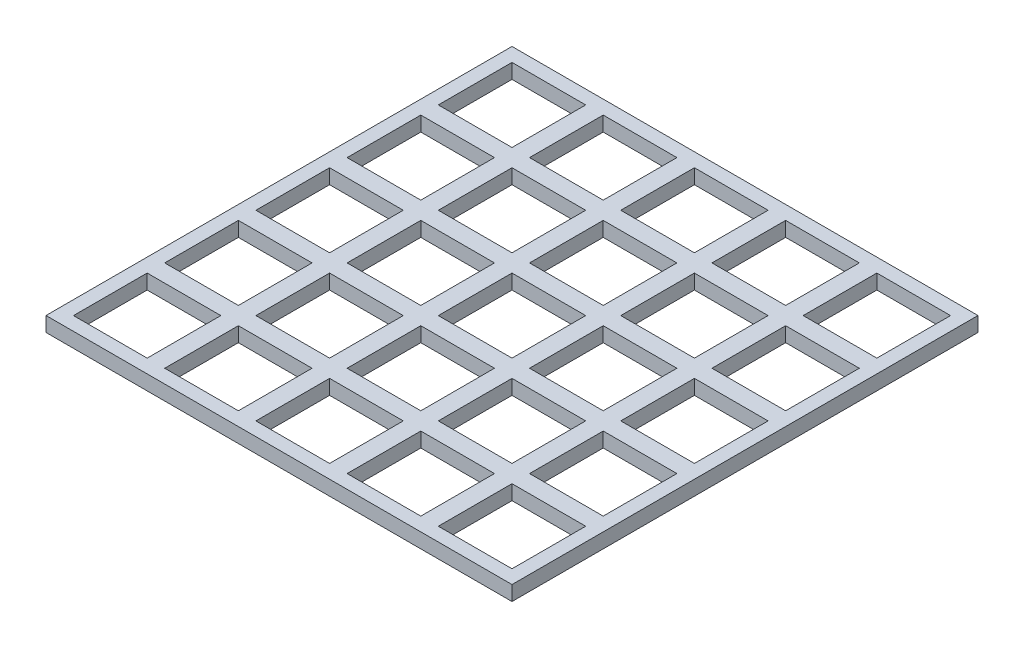
SolidWorks part; units mm, degrees
ref_plane "Front Plane" through (0, 0, 0) normal (0, 0, 1) x (1, 0, 0)
ref_plane "Top Plane" through (0, 0, 0) normal (0, 1, 0) x (1, 0, 0)
ref_plane "Right Plane" through (0, 0, 0) normal (1, 0, 0) x (0, 0, -1)
sketch "Sketch3" plane through (0, 0, 0) normal (0, 1, 0) x (1, 0, 0)
  line L0 (-17.245, 29.875) -> (-7.245, 29.875)
  line L1 (-31.5, 31.75) -> (31.75, 31.75)
  line L2 (-31.5, 31.75) -> (-31.5, -31.5)
  line L3 (-31.5, -31.5) -> (31.75, -31.5)
  line L4 (31.75, 31.75) -> (31.75, -31.5)
  line L5 (-29.625, 29.875) -> (-19.625, 29.875)
  line L6 (-29.625, 29.875) -> (-29.625, 19.875)
  line L7 (-29.625, 19.875) -> (-19.625, 19.875)
  line L8 (-19.625, 29.875) -> (-19.625, 19.875)
  line L9 (-17.245, 29.875) -> (-17.245, 19.875)
  line L10 (-17.245, 19.875) -> (-7.245, 19.875)
  line L11 (-7.245, 29.875) -> (-7.245, 19.875)
  line L12 (-4.865, 29.875) -> (5.135, 29.875)
  line L13 (-4.865, 29.875) -> (-4.865, 19.875)
  line L14 (-4.865, 19.875) -> (5.135, 19.875)
  line L15 (5.135, 29.875) -> (5.135, 19.875)
  line L16 (7.515, 29.875) -> (17.515, 29.875)
  line L17 (7.515, 29.875) -> (7.515, 19.875)
  line L18 (7.515, 19.875) -> (17.515, 19.875)
  line L19 (17.515, 29.875) -> (17.515, 19.875)
  line L20 (19.895, 29.875) -> (29.895, 29.875)
  line L21 (19.895, 29.875) -> (19.895, 19.875)
  line L22 (19.895, 19.875) -> (29.895, 19.875)
  line L23 (29.895, 29.875) -> (29.895, 19.875)
  line L24 (-17.245, 17.495) -> (-7.245, 17.495)
  line L25 (-17.245, 17.495) -> (-17.245, 7.495)
  line L26 (-17.245, 7.495) -> (-7.245, 7.495)
  line L27 (-7.245, 17.495) -> (-7.245, 7.495)
  line L28 (-4.865, 17.495) -> (5.135, 17.495)
  line L29 (-4.865, 17.495) -> (-4.865, 7.495)
  line L30 (-4.865, 7.495) -> (5.135, 7.495)
  line L31 (5.135, 17.495) -> (5.135, 7.495)
  line L32 (7.515, 17.495) -> (17.515, 17.495)
  line L33 (7.515, 17.495) -> (7.515, 7.495)
  line L34 (7.515, 7.495) -> (17.515, 7.495)
  line L35 (17.515, 17.495) -> (17.515, 7.495)
  line L36 (19.895, 17.495) -> (29.895, 17.495)
  line L37 (19.895, 17.495) -> (19.895, 7.495)
  line L38 (19.895, 7.495) -> (29.895, 7.495)
  line L39 (29.895, 17.495) -> (29.895, 7.495)
  line L40 (-17.245, 5.115) -> (-7.245, 5.115)
  line L41 (-17.245, 5.115) -> (-17.245, -4.885)
  line L42 (-17.245, -4.885) -> (-7.245, -4.885)
  line L43 (-7.245, 5.115) -> (-7.245, -4.885)
  line L44 (-4.865, 5.115) -> (5.135, 5.115)
  line L45 (-4.865, 5.115) -> (-4.865, -4.885)
  line L46 (-4.865, -4.885) -> (5.135, -4.885)
  line L47 (5.135, 5.115) -> (5.135, -4.885)
  line L48 (7.515, 5.115) -> (17.515, 5.115)
  line L49 (7.515, 5.115) -> (7.515, -4.885)
  line L50 (7.515, -4.885) -> (17.515, -4.885)
  line L51 (17.515, 5.115) -> (17.515, -4.885)
  line L52 (19.895, 5.115) -> (29.895, 5.115)
  line L53 (19.895, 5.115) -> (19.895, -4.885)
  line L54 (19.895, -4.885) -> (29.895, -4.885)
  line L55 (29.895, 5.115) -> (29.895, -4.885)
  line L56 (-17.245, -7.265) -> (-7.245, -7.265)
  line L57 (-17.245, -7.265) -> (-17.245, -17.265)
  line L58 (-17.245, -17.265) -> (-7.245, -17.265)
  line L59 (-7.245, -7.265) -> (-7.245, -17.265)
  line L60 (-4.865, -7.265) -> (5.135, -7.265)
  line L61 (-4.865, -7.265) -> (-4.865, -17.265)
  line L62 (-4.865, -17.265) -> (5.135, -17.265)
  line L63 (5.135, -7.265) -> (5.135, -17.265)
  line L64 (7.515, -7.265) -> (17.515, -7.265)
  line L65 (7.515, -7.265) -> (7.515, -17.265)
  line L66 (7.515, -17.265) -> (17.515, -17.265)
  line L67 (17.515, -7.265) -> (17.515, -17.265)
  line L68 (19.895, -7.265) -> (29.895, -7.265)
  line L69 (19.895, -7.265) -> (19.895, -17.265)
  line L70 (19.895, -17.265) -> (29.895, -17.265)
  line L71 (29.895, -7.265) -> (29.895, -17.265)
  line L72 (-17.245, -19.645) -> (-7.245, -19.645)
  line L73 (-17.245, -19.645) -> (-17.245, -29.645)
  line L74 (-17.245, -29.645) -> (-7.245, -29.645)
  line L75 (-7.245, -19.645) -> (-7.245, -29.645)
  line L76 (-4.865, -19.645) -> (5.135, -19.645)
  line L77 (-4.865, -19.645) -> (-4.865, -29.645)
  line L78 (-4.865, -29.645) -> (5.135, -29.645)
  line L79 (5.135, -19.645) -> (5.135, -29.645)
  line L80 (7.515, -19.645) -> (17.515, -19.645)
  line L81 (7.515, -19.645) -> (7.515, -29.645)
  line L82 (7.515, -29.645) -> (17.515, -29.645)
  line L83 (17.515, -19.645) -> (17.515, -29.645)
  line L84 (19.895, -19.645) -> (29.895, -19.645)
  line L85 (19.895, -19.645) -> (19.895, -29.645)
  line L86 (19.895, -29.645) -> (29.895, -29.645)
  line L87 (29.895, -19.645) -> (29.895, -29.645)
  line L88 (-29.625, 17.495) -> (-19.625, 17.495)
  line L89 (-29.625, 17.495) -> (-29.625, 7.495)
  line L90 (-29.625, 7.495) -> (-19.625, 7.495)
  line L91 (-19.625, 17.495) -> (-19.625, 7.495)
  line L92 (-29.625, 5.115) -> (-19.625, 5.115)
  line L93 (-29.625, 5.115) -> (-29.625, -4.885)
  line L94 (-29.625, -4.885) -> (-19.625, -4.885)
  line L95 (-19.625, 5.115) -> (-19.625, -4.885)
  line L96 (-29.625, -7.265) -> (-19.625, -7.265)
  line L97 (-29.625, -7.265) -> (-29.625, -17.265)
  line L98 (-29.625, -17.265) -> (-19.625, -17.265)
  line L99 (-19.625, -7.265) -> (-19.625, -17.265)
  line L100 (-29.625, -19.645) -> (-19.625, -19.645)
  line L101 (-29.625, -19.645) -> (-29.625, -29.645)
  line L102 (-29.625, -29.645) -> (-19.625, -29.645)
  line L103 (-19.625, -19.645) -> (-19.625, -29.645)
  dimension "D1" = 63.25
  dimension "D2" = 63.25
  dimension "D3" = 31.75
  dimension "D4" = 31.75
  dimension "D5" = 1.875
  dimension "D6" = 1.875
  dimension "D7" = 10
  dimension "D8" = 10
  dimension "D9" = 5
  dimension "D10" = 5
extrude "Boss-Extrude3" add sketch "Sketch3" along normal blind 2 separate body
